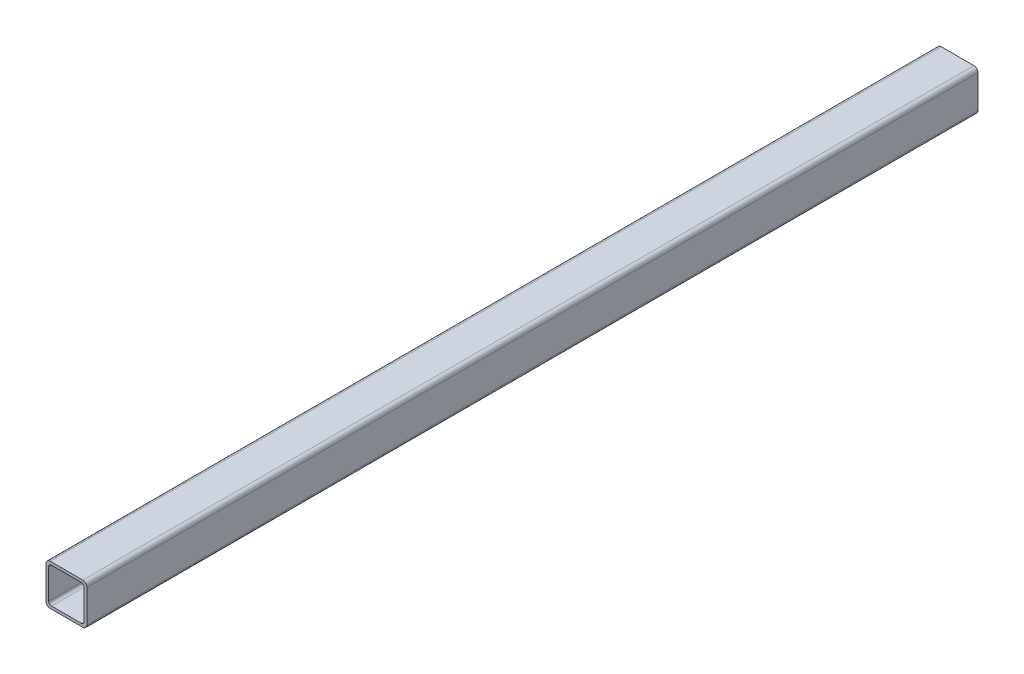
SolidWorks part; units mm, degrees
material "AISI 1020"
ref_plane "Спереди" through (0, 0, 0) normal (0, 0, 1) x (1, 0, 0)
ref_plane "Сверху" through (0, 0, 0) normal (0, 1, 0) x (1, 0, 0)
ref_plane "Справа" through (0, 0, 0) normal (1, 0, 0) x (0, 0, -1)
sketch "Эскиз1" plane through (0, 0, 0) normal (0, 0, 1) x (1, 0, 0)
  point P0 (0, 0)
  line B0 (-12, 30) -> (12, 30)
  line B1 (-15, 27) -> (-15, 3)
  line B2 (-12, 0) -> (12, 0)
  line B3 (15, 27) -> (15, 3)
  line B4 (-11, 28) -> (11, 28)
  line B5 (-13, 26) -> (-13, 4)
  line B6 (-11, 2) -> (11, 2)
  line B7 (13, 26) -> (13, 4)
  arc B8 (-15, 3) -> (-12, 0) centre (-12, 3) ccw
  arc B9 (12, 0) -> (15, 3) centre (12, 3) ccw
  arc B10 (12, 30) -> (15, 27) centre (12, 27) cw
  arc B11 (-12, 30) -> (-15, 27) centre (-12, 27) ccw
  arc B12 (-13, 4) -> (-11, 2) centre (-11, 4) ccw
  arc B13 (11, 2) -> (13, 4) centre (11, 4) ccw
  arc B14 (11, 28) -> (13, 26) centre (11, 26) cw
  arc B15 (-11, 28) -> (-13, 26) centre (-11, 26) ccw
sketch_block_instance "Блок-30х30х2-1"
sketch_block "Блок-30х30х2" parameters "D3"=3, "D4"=2, "D1"=30, "D2"=2
extrude "Бобышка-Вытянуть1" add sketch "Эскиз1" along normal offset from surface (327 mm away) 6
mirror "Зеркальное отражение2" about plane through (-12, 3, 0) normal (0, 0, 1) of bodies 103
